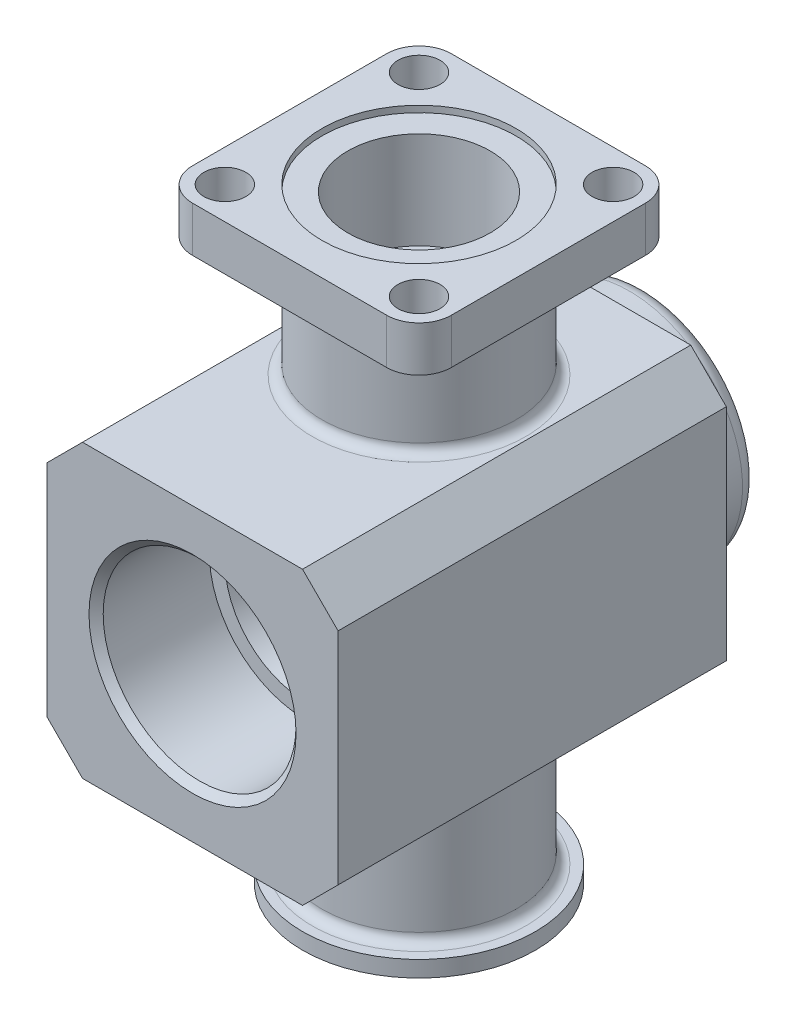
SolidWorks part; units mm, degrees
material "Бронза"
ref_plane "Спереди" through (0, 0, 0) normal (0, 0, 1) x (1, 0, 0)
ref_plane "Сверху" through (0, 0, 0) normal (0, 1, 0) x (1, 0, 0)
ref_plane "Справа" through (0, 0, 0) normal (1, 0, 0) x (0, 0, -1)
sketch "Эскиз1" plane through (0, 0, 0) normal (0, 0, 1) x (1, 0, 0)
  line L1 (-45, -45) -> (45, -45)
  line L2 (-45, -45) -> (-45, 45)
  line L3 (-45, 45) -> (45, 45)
  line L4 (45, -45) -> (45, 45)
  line L5 (-45, -45) -> (45, 45) construction
  line L6 (-45, 45) -> (45, -45) construction
  point P0 (0, 0)
  dimension "D1" = 90
extrude "Бобышка-Вытянуть1" add sketch "Эскиз1" along normal blind 120
sketch "Эскиз9" plane through (0, 0, 0) normal (0, 0, -1) x (-1, 0, 0)
  circle A0 centre (0, 0) radius 35
  dimension "D1" = 70
extrude "Бобышка-Вытянуть6" add sketch "Эскиз9" along normal blind 20
sketch "Эскиз2" plane through (0, 45, 0) normal (0, 1, 0) x (1, 0, 0)
  line L0 (0, 20) -> (0, -120) construction
  line L1 (45, -120) -> (-45, -120) construction
  line L2 (35, 20) -> (-35, 20) construction
  circle A0 centre (0, -50) radius 30
  dimension "D1" = 60
extrude "Бобышка-Вытянуть2" add sketch "Эскиз2" along normal blind 51
sketch "Эскиз3" plane through (0, 96, 0) normal (0, 1, 0) x (1, 0, 0)
  line L1 (-40, -90) -> (40, -90)
  line L2 (-40, -90) -> (-40, -10)
  line L3 (-40, -10) -> (40, -10)
  line L4 (40, -90) -> (40, -10)
  line L5 (-40, -90) -> (40, -10) construction
  line L6 (-40, -10) -> (40, -90) construction
  point P0 (0, -50)
  dimension "D1" = 80
extrude "Бобышка-Вытянуть3" add sketch "Эскиз3" against normal blind 14
sketch "Эскиз4" plane through (0, -45, 0) normal (0, -1, 0) x (1, 0, 0)
  line L0 (0, 120) -> (0, -20) construction
  line L1 (-45, 120) -> (45, 120) construction
  line L2 (-35, -20) -> (35, -20) construction
  circle A0 centre (0, 50) radius 30
  dimension "D1" = 60
extrude "Бобышка-Вытянуть4" add sketch "Эскиз4" along normal blind 46
sketch "Эскиз5" plane through (0, -91, 0) normal (0, -1, 0) x (1, 0, 0)
  circle A0 centre (0, 50) radius 36
  dimension "D1" = 72
extrude "Бобышка-Вытянуть5" add sketch "Эскиз5" against normal blind 5
sketch "Эскиз6" plane through (0, -91, 0) normal (0, -1, 0) x (-1, 0, 0)
  circle A0 centre (0, -50) radius 15
  dimension "D1" = 30
extrude "Вырез-Вытянуть1" cut sketch "Эскиз6" against normal through all
sketch "Эскиз7" plane through (0, 96, 0) normal (0, 1, 0) x (1, 0, 0)
  circle A0 centre (0, -50) radius 22
  dimension "D1" = 44
extrude "Вырез-Вытянуть2" cut sketch "Эскиз7" against normal blind 32
sketch "Эскиз8" plane through (0, -91, 0) normal (0, -1, 0) x (1, 0, 0)
  circle A0 centre (0, 50) radius 22.352
  dimension "D1" = 44.704
extrude "Вырез-Вытянуть3" cut sketch "Эскиз8" against normal blind 36
cosmetic thread "Условное изображение резьбы2" parameters "D1"=28, "D2"=48
fillet "Скругление1" radius 10 4 edges at (-40, 89, 10) (40, 89, 10) (40, 89, 90) (-40, 89, 90)
sketch "Эскиз10" plane through (0, 96, 0) normal (0, 1, 0) x (1, 0, 0)
  line L1 (-30, -80) -> (30, -80) construction
  line L2 (-30, -80) -> (-30, -20) construction
  line L3 (-30, -20) -> (30, -20) construction
  line L4 (30, -80) -> (30, -20) construction
  line L5 (-30, -80) -> (30, -20) construction
  line L6 (-30, -20) -> (30, -80) construction
  circle A0 centre (-30, -20) radius 6.5
  circle A1 centre (30, -80) radius 6.5
  circle A2 centre (30, -20) radius 6.5
  circle A3 centre (-30, -80) radius 6.5
  point P2 (0, -50)
  dimension "D2" = 13
  dimension "D1" = 60
extrude "Вырез-Вытянуть4" cut sketch "Эскиз10" against normal up to surface (14 mm away) up to face at (0, 82, 50)
chamfer "Фаска1" distance 11 angle 45 4 edges at (45, -45, 60) (-45, -45, 60) (-45, 45, 60) (45, 45, 60)
fillet "Скругление2" radius 5 2 edges at (-35, 0, 0) (-35, 0, -20)
sketch "Эскиз11" plane through (0, 0, 120) normal (0, 0, 1) x (1, 0, 0)
  circle A0 centre (0, 0) radius 29.805
  dimension "D1" = 59.61
extrude "Вырез-Вытянуть5" cut sketch "Эскиз11" against normal blind 35 contours A0
cosmetic thread "Условное изображение резьбы1" parameters "D1"=20, "D2"=64
sketch "Эскиз13" plane through (0, 0, 0) normal (1, 0, 0) x (0, 0, -1)
  line L0 (0, 0) -> (-120, 0) construction
  line L1 (0, 34) -> (0, -34) construction
  line L2 (-120, 29.805) -> (-120, -29.805) construction
  line L3 (-85, 25) -> (5, 12.3513)
  line L4 (-85, 29.805) -> (-85, -29.805) construction
  line L5 (5, 12.3513) -> (5, 0)
  line L6 (5, 0) -> (-85, 0)
  line L7 (-85, 0) -> (-85, 25)
  dimension "D1" = 50
  dimension "D2" = 90
  dimension "D3" = 8
revolve "Вырез-Повернуть1" cut sketch "Эскиз13" angle 360 about L0
chamfer "Фаска2" distance 2.195 angle 45 1 edges at (29.805, 0, 120)
sketch "Эскиз14" plane through (0, 96, 0) normal (0, 1, 0) x (1, 0, 0)
  circle A0 centre (0, -50) radius 30
  point P0 (0, -50)
  dimension "D1" = 60
extrude "Вырез-Вытянуть6" cut sketch "Эскиз14" against normal blind 2
fillet "Скругление3" radius 3 4 edges at (0, 82, 20) (0, -86, 20) (0, -45, 80) (0, 45, 20)
chamfer "Фаска4" distance 1.648 angle 45 1 edges at (0, -91, 27.648)
